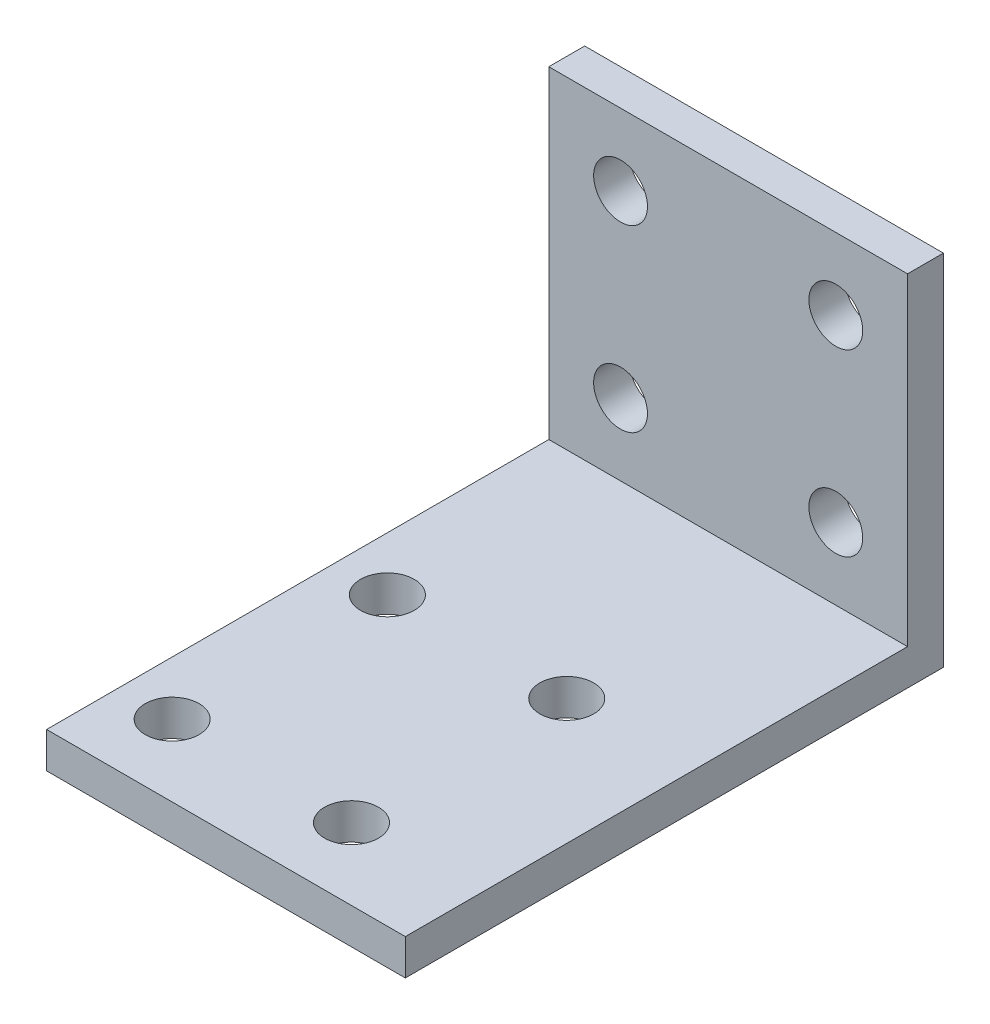
SolidWorks part; units mm, degrees
ref_plane "前视基准面" through (0, 0, 0) normal (0, 0, 1) x (1, 0, 0)
ref_plane "上视基准面" through (0, 0, 0) normal (0, 1, 0) x (1, 0, 0)
ref_plane "右视基准面" through (0, 0, 0) normal (1, 0, 0) x (0, 0, -1)
sketch "草图1" plane through (0, 0, 0) normal (0, 1, 0) x (1, 0, 0)
  line L1 (-21.3353, 6.9139) -> (8.6647, 6.9139)
  line L2 (-21.3353, 6.9139) -> (-21.3353, -33.0861)
  line L3 (-21.3353, -33.0861) -> (8.6647, -33.0861)
  line L4 (8.6647, 6.9139) -> (8.6647, -33.0861)
  dimension "D1" = 30
  dimension "D2" = 40
extrude "凸台-拉伸1" add sketch "草图1" along normal blind 3
sketch "草图2" plane through (0, 3, 0) normal (0, 1, 0) x (1, 0, 0)
  line L0 (8.6647, -33.0861) -> (8.6647, 6.9139) construction
  line L1 (-21.3353, 6.9139) -> (8.6647, 6.9139)
  line L2 (-21.3353, 6.9139) -> (-21.3353, 3.9139)
  line L3 (-21.3353, 3.9139) -> (8.6647, 3.9139)
  line L4 (8.6647, 6.9139) -> (8.6647, 3.9139)
  dimension "D1" = 3
extrude "凸台-拉伸2" add sketch "草图2" along normal blind 17
sketch "草图5" plane through (8.6647, 0, 0) normal (1, 0, 0) x (0, 0, -1)
  line L1 (3.9139, 20) -> (6.9139, 20)
  line L2 (3.9139, 20) -> (3.9139, 0)
  line L3 (3.9139, 0) -> (6.9139, 0)
  line L4 (6.9139, 20) -> (6.9139, 0)
  line L5 (3.9139, 0) -> (-33.0861, 0)
  line L6 (3.9139, 0) -> (3.9139, 3)
  line L7 (3.9139, 3) -> (-33.0861, 3)
  line L8 (-33.0861, 0) -> (-33.0861, 3)
  line M1 (-33.0861, 0) -> (6.9139, 0)
  line M2 (6.9139, 0) -> (6.9139, 20)
  line M3 (6.9139, 20) -> (3.9139, 20)
  line M4 (3.9139, 20) -> (3.9139, 3)
  line M5 (3.9139, 3) -> (-33.0861, 3)
  line M6 (-33.0861, 3) -> (-33.0861, 0)
extrude "切除-拉伸3" cut sketch "草图5" against normal blind 10 contours L2 M4 M1 M2 M3 | L2 M5 M6 M1
sketch "草图6" plane through (0, 0, 33.0861) normal (0, 0, 1) x (1, 0, 0)
  line L1 (-21.3353, 3) -> (-1.3353, 3)
  line L2 (-21.3353, 3) -> (-21.3353, 0)
  line L3 (-21.3353, 0) -> (-1.3353, 0)
  line L4 (-1.3353, 3) -> (-1.3353, 0)
extrude "切除-拉伸4" cut sketch "草图6" against normal blind 10
sketch "草图7" plane through (0, 0, -3.9139) normal (0, 0, 1) x (1, 0, 0)
  line L1 (-21.3353, 20) -> (-1.3353, 20)
  line L2 (-21.3353, 20) -> (-21.3353, 3)
  line L3 (-21.3353, 3) -> (-1.3353, 3)
  line L4 (-1.3353, 20) -> (-1.3353, 3)
extrude "切除-拉伸5" cut sketch "草图7" against normal blind 1
sketch "草图8" plane through (0, 3, 0) normal (0, 1, 0) x (1, 0, 0)
  line L1 (-1.3353, 4.9139) -> (-21.3353, 4.9139)
  line L2 (-1.3353, 4.9139) -> (-1.3353, -23.0861)
  line L3 (-1.3353, -23.0861) -> (-21.3353, -23.0861)
  line L4 (-21.3353, 4.9139) -> (-21.3353, -23.0861)
extrude "切除-拉伸6" cut sketch "草图8" against normal blind 1
sketch "草图10" plane through (0, 0, 0) normal (0, -1, 0) x (1, 0, 0)
  circle A0 centre (-8.3353, 7.0861) radius 1.5
  circle A1 centre (-8.3353, 19.0861) radius 1.5
  circle A2 centre (-18.3353, 7.0861) radius 1.5
  circle A3 centre (-18.3353, 19.0861) radius 1.5
extrude "切除-拉伸7" cut sketch "草图10" against normal blind 10
sketch "草图11" plane through (0, 0, -4.9139) normal (0, 0, 1) x (1, 0, 0)
  line L0 (-1.3353, 2) -> (-1.3353, 20) construction
  line L1 (-21.3353, 20) -> (-21.3353, 2) construction
  line L2 (-1.3353, 2) -> (-21.3353, 2) construction
  line L3 (-1.3353, 20) -> (-21.3353, 20) construction
  circle A0 centre (-5.3353, 6) radius 1.5
  circle A1 centre (-17.3353, 6) radius 1.5
  circle A2 centre (-5.3353, 16) radius 1.5
  circle A3 centre (-17.3353, 16) radius 1.5
  dimension "D1" = 4
  dimension "D9" = 3
  dimension "D10" = 3
  dimension "D11" = 3
  dimension "D12" = 3
  dimension "D2" = 4
  dimension "D3" = 4
  dimension "D4" = 4
  dimension "D5" = 4
  dimension "D6" = 4
  dimension "D7" = 4
  dimension "D8" = 4
extrude "切除-拉伸8" cut sketch "草图11" against normal blind 10
